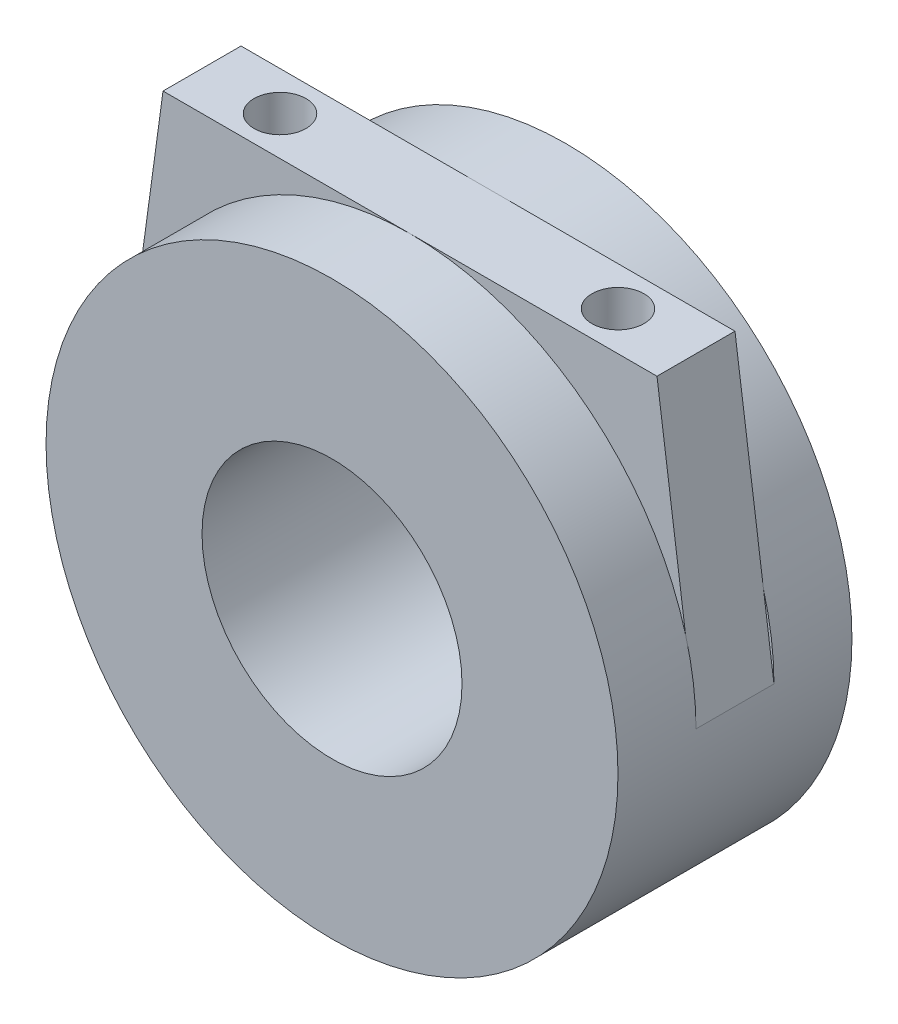
SolidWorks part; units mm, degrees
ref_plane "Front Plane" through (0, 0, 0) normal (0, 0, 1) x (1, 0, 0)
ref_plane "Top Plane" through (0, 0, 0) normal (0, 1, 0) x (1, 0, 0)
ref_plane "Right Plane" through (0, 0, 0) normal (1, 0, 0) x (0, 0, -1)
sketch "Sketch1" plane through (0, 0, 0) normal (0, 0, 1) x (1, 0, 0)
  circle A0 centre (0, 0) radius 11
  dimension "D1" = 22
extrude "Boss-Extrude1" add sketch "Sketch1" along normal blind 3
sketch "Sketch2" plane through (0, 0, 3) normal (0, 0, 1) x (1, 0, 0)
  line L0 (-11, 0) -> (-9.5, 11)
  line L1 (-9.5, 11) -> (9.5, 11)
  line L2 (9.5, 11) -> (11, 0)
  line L3 (0, 11) -> (0, 0) construction
  arc A0 (-11, 0) -> (11, 0) centre (0, 0) ccw
  point P5 (0, 0)
  point P8 (9.5, 11)
  point P9 (0, 11)
  dimension "D1" = 19
  dimension "D2" = 11
extrude "Boss-Extrude2" add sketch "Sketch2" along normal blind 3
sketch "Sketch3" plane through (0, 0, 6) normal (0, 0, 1) x (1, 0, 0)
  circle A0 centre (0, 0) radius 11
extrude "Boss-Extrude3" add sketch "Sketch3" along normal blind 3
sketch "Sketch4" plane through (0, 0, 9) normal (0, 0, 1) x (1, 0, 0)
  circle A0 centre (0, 0) radius 5
extrude "Cut-Extrude1" cut sketch "Sketch4" against normal through all
sketch "Sketch5" plane through (0, 11, 0) normal (0, 1, 0) x (1, 0, 0)
  line L0 (-6.5, -4.5) -> (6.5, -4.5) construction
  line L1 (0, -4.5) -> (0, -6) construction
  circle A0 centre (-6.5, -4.5) radius 1
  circle A1 centre (6.5, -4.5) radius 1
  dimension "D1" = 13
extrude "Cut-Extrude2" cut sketch "Sketch5" against normal blind 3
